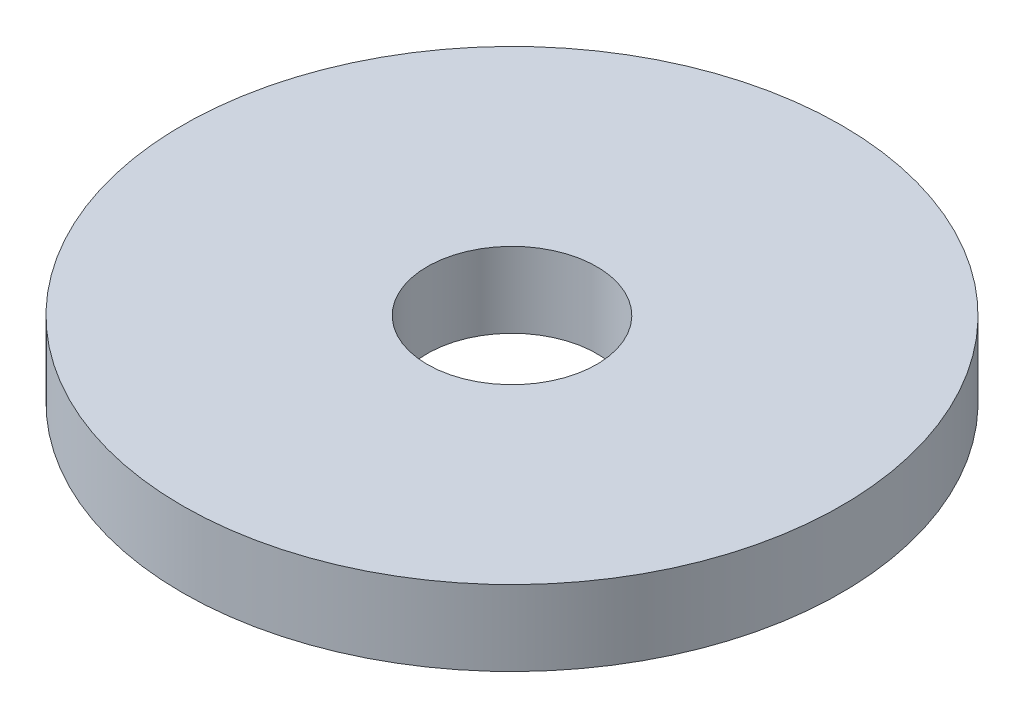
SolidWorks part; units mm, degrees
ref_plane "前视基准面" through (0, 0, 0) normal (0, 0, 1) x (1, 0, 0)
ref_plane "上视基准面" through (0, 0, 0) normal (0, 1, 0) x (1, 0, 0)
ref_plane "右视基准面" through (0, 0, 0) normal (1, 0, 0) x (0, 0, -1)
sketch "Sketch1" plane through (0, 0, 0) normal (0, 1, 0) x (1, 0, 0)
  circle A0 centre (0, 0) radius 0.9
  circle A1 centre (0, 0) radius 3.5
  dimension "D1" = 1.8
  dimension "D2" = 7
extrude "Extrude1" add sketch "Sketch1" along normal blind 0.8
